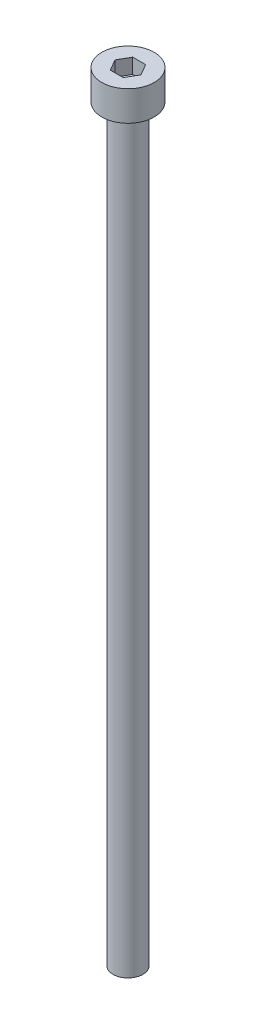
SolidWorks part; units mm, degrees
material "AISI 304"
ref_plane "前视基准面" through (0, 0, 0) normal (0, 0, 1) x (1, 0, 0)
ref_plane "上视基准面" through (0, 0, 0) normal (0, 1, 0) x (1, 0, 0)
ref_plane "右视基准面" through (0, 0, 0) normal (1, 0, 0) x (0, 0, -1)
sketch "草图1" plane through (0, 0, 0) normal (0, 1, 0) x (1, 0, 0)
  circle A0 centre (0, 0) radius 3.5
  dimension "D1" = 7
extrude "杯头" add sketch "草图1" along normal blind 4
sketch "草图2" plane through (0, 4, 0) normal (0, 1, 0) x (1, 0, 0)
  line L1 (1.7321, 0) -> (0.866, 1.5)
  line L2 (0.866, 1.5) -> (-0.866, 1.5)
  line L3 (-0.866, 1.5) -> (-1.7321, 0)
  line L4 (-1.7321, 0) -> (-0.866, -1.5)
  line L5 (-0.866, -1.5) -> (0.866, -1.5)
  line L6 (0.866, -1.5) -> (1.7321, 0)
  circle A0 centre (0, 0) radius 1.5 construction
  dimension "D1" = 3
extrude "内六角口" cut sketch "草图2" against normal blind 2
sketch "草图3" plane through (0, 0, 0) normal (0, -1, 0) x (1, 0, 0)
  circle A0 centre (0, 0) radius 2
  dimension "D1" = 4
extrude "螺纹长度" add sketch "草图3" along normal blind 100
